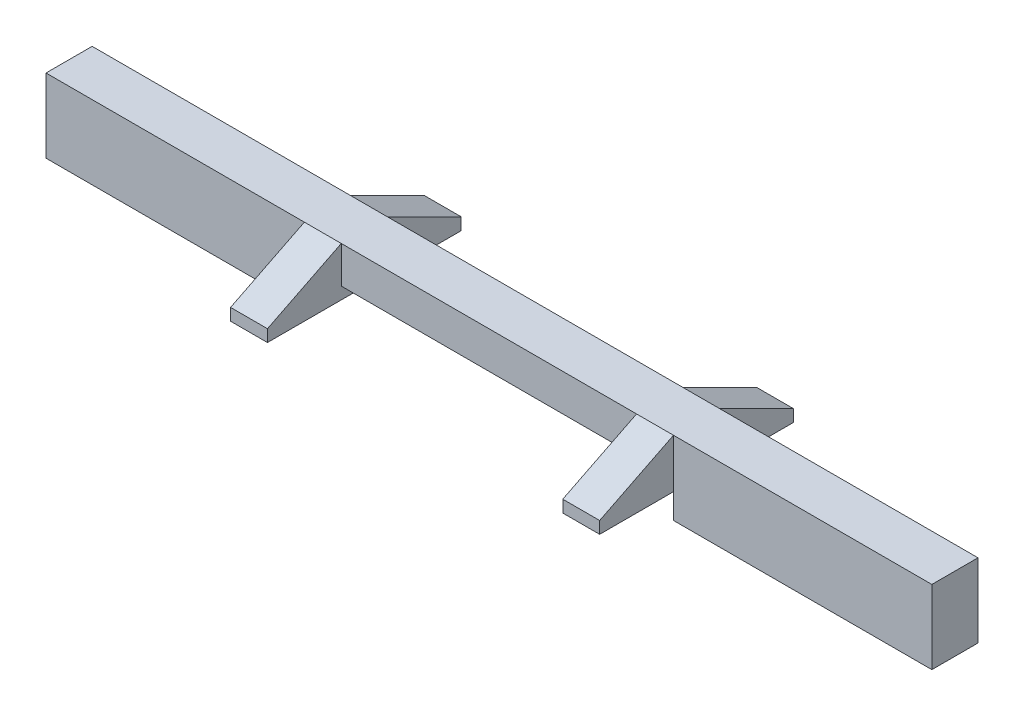
SolidWorks part; units mm, degrees
ref_plane "Front Plane" through (0, 0, 0) normal (0, 0, 1) x (1, 0, 0)
ref_plane "Top Plane" through (0, 0, 0) normal (0, 1, 0) x (1, 0, 0)
ref_plane "Right Plane" through (0, 0, 0) normal (1, 0, 0) x (0, 0, -1)
sketch "Sketch1" plane through (0, 0, 0) normal (0, 0, 1) x (1, 0, 0)
  line L10 (1, 0) -> (9, 0)
  line L12 (0, 1) -> (10, 1)
  line L14 (0, 1) -> (-7, 1)
  line L15 (0, -0.325) -> (0, -1)
  line L16 (0, -1) -> (-7, -1)
  line L17 (-7, 1) -> (-7, -1)
  line L18 (10, 1) -> (17, 1)
  line L19 (10, -0.325) -> (10, -1)
  line L20 (10, -1) -> (17, -1)
  line L21 (17, 1) -> (17, -1)
  line L24 (0, -0.325) -> (1, -0.325)
  line L25 (1, 0) -> (1, -0.325)
  line L28 (10, -0.325) -> (9, -0.325)
  line L29 (9, 0) -> (9, -0.325)
extrude "Boss-Extrude1" add sketch "Sketch1" along normal blind 1.25
sketch "Sketch2" plane through (0, 0, 1.25) normal (0, 0, 1) x (1, 0, 0)
  line L1 (1, -0.325) -> (0, -0.325)
  line L2 (1, -0.325) -> (1, 0)
  line L3 (1, 0) -> (0, 0)
  line L4 (0, -0.325) -> (0, 0)
  line L5 (9, -0.325) -> (10, -0.325)
  line L6 (9, -0.325) -> (9, 0)
  line L7 (9, 0) -> (10, 0)
  line L8 (10, -0.325) -> (10, 0)
  dimension "D1" = 0.325
  dimension "D2" = 1
extrude "Boss-Extrude2" add sketch "Sketch2" along normal blind 2
sketch "Sketch3" plane through (0, 0, 0) normal (0, 0, -1) x (-1, 0, 0)
  line L1 (-9, -0.325) -> (-10, -0.325)
  line L2 (-9, -0.325) -> (-9, 0)
  line L3 (-9, 0) -> (-10, 0)
  line L4 (-10, -0.325) -> (-10, 0)
  line L5 (-1, -0.325) -> (0, -0.325)
  line L6 (-1, -0.325) -> (-1, 0)
  line L7 (-1, 0) -> (0, 0)
  line L8 (0, -0.325) -> (0, 0)
  dimension "D1" = 1
  dimension "D2" = 0.325
  dimension "D3" = 1
  dimension "D4" = 0.325
extrude "Boss-Extrude3" add sketch "Sketch3" along normal blind 2
sketch "Sketch7" plane through (10, 0, 0) normal (1, 0, 0) x (0, 0, -1)
  line L0 (-3.25, 0) -> (-1.25, 1)
  line L1 (-1.25, 1) -> (-1.25, 0)
  line L2 (2, 0) -> (0, 1)
  line L3 (0, 1) -> (0, 0)
  line L4 (0, 0) -> (2, 0)
  line L6 (-1.25, -0.325) -> (-1.25, 0)
  line L7 (-1.25, 0) -> (-3.25, 0)
  line L8 (-3.25, 0) -> (-3.25, -0.325)
  line L9 (-3.25, -0.325) -> (-1.25, -0.325)
  line L10 (-1.25, -0.325) -> (-1.25, 0)
  line L12 (-3.25, 0) -> (-3.25, -0.325)
  line L13 (-3.25, -0.325) -> (-1.25, -0.325)
  dimension "D1" = 0
extrude "Boss-Extrude7" add sketch "Sketch7" against normal blind 1
sketch "Sketch8" plane through (0, 0, 0) normal (-1, 0, 0) x (0, 0, 1)
  line L0 (-2, 0) -> (0, 1)
  line L1 (0, 1) -> (0, 0)
  line L2 (0, 0) -> (-2, 0)
  line L3 (1.25, 1) -> (1.25, 0)
  line L4 (1.25, 0) -> (3.25, 0)
  line L5 (3.25, 0) -> (1.25, 1)
extrude "Boss-Extrude8" add sketch "Sketch8" against normal blind 1
